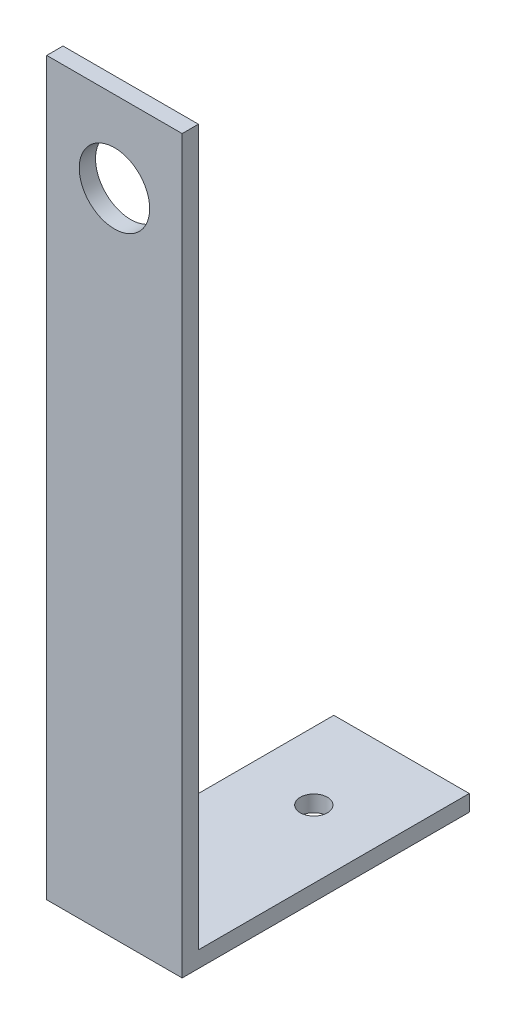
SolidWorks part; units mm, degrees
material "AISI 1030 HR"
ref_plane "Alzado" through (0, 0, 0) normal (0, 0, 1) x (1, 0, 0)
ref_plane "Planta" through (0, 0, 0) normal (0, 1, 0) x (1, 0, 0)
ref_plane "Vista lateral" through (0, 0, 0) normal (1, 0, 0) x (0, 0, -1)
sketch "Croquis1" plane through (0, 0, 0) normal (0, 1, 0) x (1, 0, 0)
  line L1 (-25, -50) -> (25, -50)
  line L2 (-25, -50) -> (-25, 50)
  line L3 (-25, 50) -> (25, 50)
  line L4 (25, -50) -> (25, 50)
  line L5 (-25, -50) -> (25, 50) construction
  line L6 (-25, 50) -> (25, -50) construction
  point P0 (0, 0)
  dimension "D1" = 50
  dimension "D2" = 100
extrude "Saliente-Extruir1" add sketch "Croquis1" along normal blind 6
sketch "Croquis2" plane through (0, 0, 0) normal (0, -1, 0) x (1, 0, 0)
  line L1 (25, 50) -> (-25, 50)
  line L2 (25, 50) -> (25, 56)
  line L3 (25, 56) -> (-25, 56)
  line L4 (25, -50) -> (25, 50)
  line L5 (25, 50) -> (-25, 50)
  line L6 (-25, 50) -> (-25, -50)
  line L7 (-25, -50) -> (25, -50)
  line L8 (25, -50) -> (25, 50)
  line L9 (25, 50) -> (-25, 50)
  line L10 (-25, 50) -> (-25, -50)
  line L11 (-25, -50) -> (25, -50)
  line L12 (-25, 50) -> (-25, 56)
  line M10 (25, 50) -> (-25, 50)
  dimension "D2" = 6
  dimension "D1" = 0
extrude "Saliente-Extruir2" add sketch "Croquis2" against normal blind 270 contours L12 L2 L3 M10
sketch "Croquis3" plane through (0, 0, 56) normal (0, 0, 1) x (1, 0, 0)
  line L0 (25, 270) -> (-25, 270) construction
  line L1 (25, 270) -> (25, 0) construction
  circle A0 centre (0, 240) radius 13
  dimension "D1" = 26
  dimension "D2" = 30
  dimension "D3" = 25
extrude "Cortar-Extruir1" cut sketch "Croquis3" against normal through all
sketch "Sketch1" plane through (0, 6, 0) normal (0, 1, 0) x (1, 0, 0)
  circle A0 centre (0, 17.6164) radius 5
  dimension "D1" = 10
extrude "Cut-Extrude1" cut sketch "Sketch1" against normal blind 10
